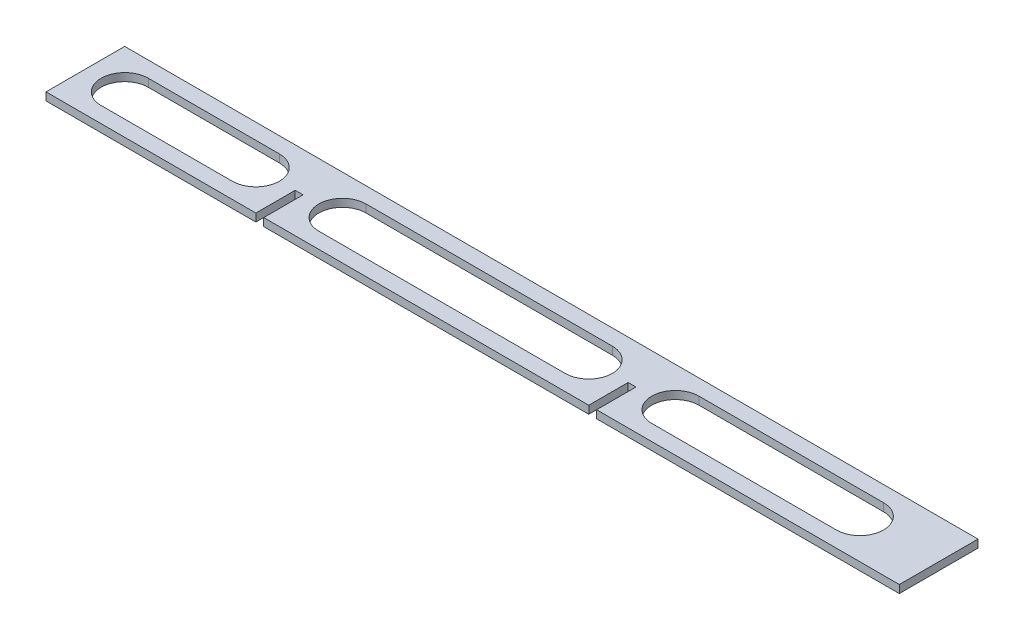
SolidWorks part; units mm, degrees
material "Pine"
ref_plane "Front Plane" through (0, 0, 0) normal (0, 0, 1) x (1, 0, 0)
ref_plane "Top Plane" through (0, 0, 0) normal (0, 1, 0) x (1, 0, 0)
ref_plane "Right Plane" through (0, 0, 0) normal (1, 0, 0) x (0, 0, -1)
sketch "Sketch1" plane through (0, 0, 0) normal (0, 1, 0) x (1, 0, 0)
  line L1 (0, 15) -> (325.28, 15)
  line L2 (0, 15) -> (0, -15)
  line L3 (0, -15) -> (325.28, -15)
  line L4 (325.28, 15) -> (325.28, -15)
  point P4 (0, 0)
  dimension "D1" = 30
  dimension "D2" = 325.28
extrude "Boss-Extrude1" add sketch "Sketch1" along normal blind 3
sketch "Sketch2" plane through (0, 3, 0) normal (0, 1, 0) x (1, 0, 0)
  line L0 (0, -15) -> (325.28, -15) construction
  line L1 (80, -15) -> (83, -15)
  line L2 (80, -15) -> (80, 0)
  line L3 (80, 0) -> (83, 0)
  line L4 (83, -15) -> (83, 0)
  line L5 (0, 15) -> (0, -15) construction
  line L18 (0, -15) -> (325.28, -15) construction
  line L19 (206.9, -15) -> (209.9, -15)
  line L20 (206.9, -15) -> (206.9, 0)
  line L25 (206.9, 0) -> (209.9, 0)
  line L26 (209.9, -15) -> (209.9, 0)
  line L27 (325.28, -15) -> (325.28, 15) construction
  line L28 (325.28, -7.5) -> (325.28, 7.5) construction
  point P14 (81.5, 0)
  point P17 (208.4, 0)
  point P21 (325.28, 0)
  dimension "D1" = 15
  dimension "D2" = 3
  dimension "D3" = 80
  dimension "D5" = 126.9
  dimension "D6" = 15
  dimension "D4" = 243.78
extrude "Cut-Extrude1" cut sketch "Sketch2" against normal through all both
sketch "Sketch4" plane through (0, 3, 0) normal (0, 1, 0) x (1, 0, 0)
  line L0 (0, 0) -> (15, 0) construction
  line L1 (325.28, 0) -> (310.28, 0) construction
  line L2 (325.28, -15) -> (325.28, 15) construction
  line L3 (80, 0) -> (65, 0) construction
  line L6 (310.28, 0) -> (295.28, 0) construction
  line L7 (80, 0) -> (80, -15) construction
  line L8 (15, 0) -> (65, 0) construction
  line L9 (15, 9) -> (65, 9)
  line L10 (15, -9) -> (65, -9)
  line L11 (83, 0) -> (98, 0) construction
  line L12 (83, -15) -> (83, 0) construction
  line L13 (206.9, 0) -> (191.9, 0) construction
  line L14 (206.9, 0) -> (206.9, -15) construction
  line L15 (209.9, 0) -> (224.9, 0) construction
  line L17 (209.9, -15) -> (209.9, 0) construction
  line L19 (98, 0) -> (191.9, 0) construction
  line L20 (98, 9) -> (191.9, 9)
  line L21 (98, -9) -> (191.9, -9)
  line L22 (224.9, 0) -> (295.28, 0) construction
  line L25 (224.9, 9) -> (295.28, 9)
  line L26 (224.9, -9) -> (295.28, -9)
  arc A2 (15, 9) -> (15, -9) centre (15, 0) ccw
  arc A3 (65, -9) -> (65, 9) centre (65, 0) ccw
  arc A4 (98, 9) -> (98, -9) centre (98, 0) ccw
  arc A5 (191.9, -9) -> (191.9, 9) centre (191.9, 0) ccw
  arc A8 (224.9, 9) -> (224.9, -9) centre (224.9, 0) ccw
  arc A9 (295.28, -9) -> (295.28, 9) centre (295.28, 0) ccw
  point P6 (40, 0)
  point P28 (144.95, 0)
  point P34 (260.09, 0)
  dimension "D1" = 15
  dimension "D2" = 9
  dimension "D3" = 15
extrude "Cut-Extrude3" cut sketch "Sketch4" against normal through all
